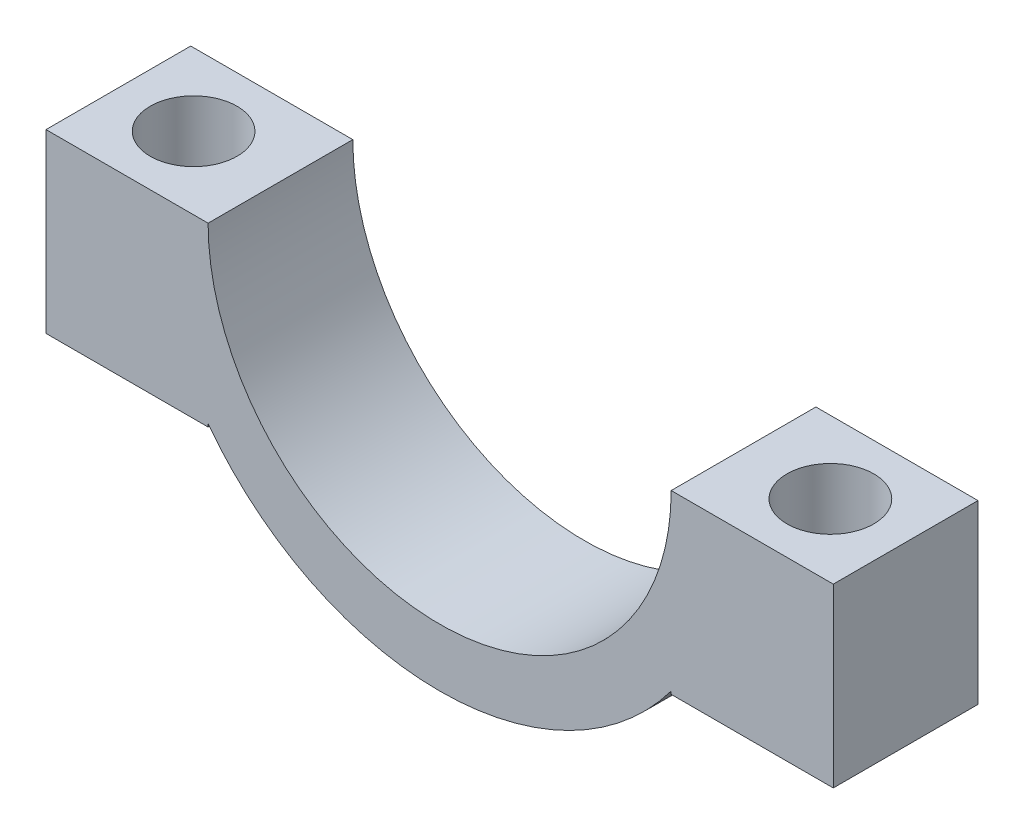
SolidWorks part; units mm, degrees
material "1060 Alloy"
ref_plane "Front Plane" through (0, 0, 0) normal (0, 0, 1) x (1, 0, 0)
ref_plane "Top Plane" through (0, 0, 0) normal (0, 1, 0) x (1, 0, 0)
ref_plane "Right Plane" through (0, 0, 0) normal (1, 0, 0) x (0, 0, -1)
sketch "Sketch2" plane through (0, 0, 0) normal (0, 0, 1) x (1, 0, 0)
  line L0 (-1000, 0) -> (49000, 0) construction
  line L1 (-8, 0) -> (-13.6, 0)
  line L2 (-13.6, 0) -> (-13.6, 10)
  line L3 (-13.6, 10) -> (-8, 10)
  line L4 (-8, 10) -> (-8, 0)
  line L5 (0, -1000) -> (0, 49000) construction
  line L6 (8, 0) -> (13.6, 0)
  line L7 (13.6, 0) -> (13.6, 10)
  line L8 (13.6, 10) -> (8, 10)
  line L9 (8, 10) -> (8, 0)
  line L11 (-13.6, 0) -> (-8, 0)
  line L12 (-13.6, 0) -> (-13.6, -6.1)
  line L13 (-13.6, -6.1) -> (-8, -6.1)
  line L14 (-8, 0) -> (-8, -6.1)
  line L15 (13.6, 0) -> (8, 0)
  line L16 (13.6, 0) -> (13.6, -6.1)
  line L17 (13.6, -6.1) -> (8, -6.1)
  line L18 (8, 0) -> (8, -6.1)
  circle A0 centre (0, 0) radius 8
  circle A1 centre (0, 0) radius 10
  circle A2 centre (-5.5966, 11.6315) radius 2.9079
  circle A3 centre (5.6058, 11.6315) radius 2.9079
  spline S0 degree 1 poles (-8, 10) (0, 10) knots 0 0 1 1
  dimension "D1" = 16
  dimension "D2" = 20
  dimension "D5" = 10
  dimension "D3" = 5.6
  dimension "D4" = 10
  dimension "D6" = 5.6
  dimension "D7" = 6.1
  dimension "D8" = 6.1
extrude "Boss-Extrude1" add sketch "Sketch2" along normal blind 5 contours A1 L11 L12 L13 L14 | L1 A1 L14 | L14 A1 L18 A0 | L18 A1 L6 | A1 L18 L17 L16 L15
sketch "Sketch3" plane through (0, 0, 0) normal (0, 1, 0) x (1, 0, 0)
  line L0 (-43.8792, -2.5) -> (17.8792, -2.5) construction
  line L1 (0, -1000) -> (0, 49000) construction
  line L2 (-11, -1003.1301) -> (-11, 48996.8699) construction
  line L3 (11, -1002.7941) -> (11, 48997.2059) construction
  circle A0 centre (-11, -2.5) radius 1.5
  circle A1 centre (11, -2.5) radius 1.5
  point P3 (-13, -2.5)
  dimension "D4" = 3
  dimension "D1" = 11
  dimension "D2" = 11
extrude "Cut-Extrude1" cut sketch "Sketch3" against normal blind 10
